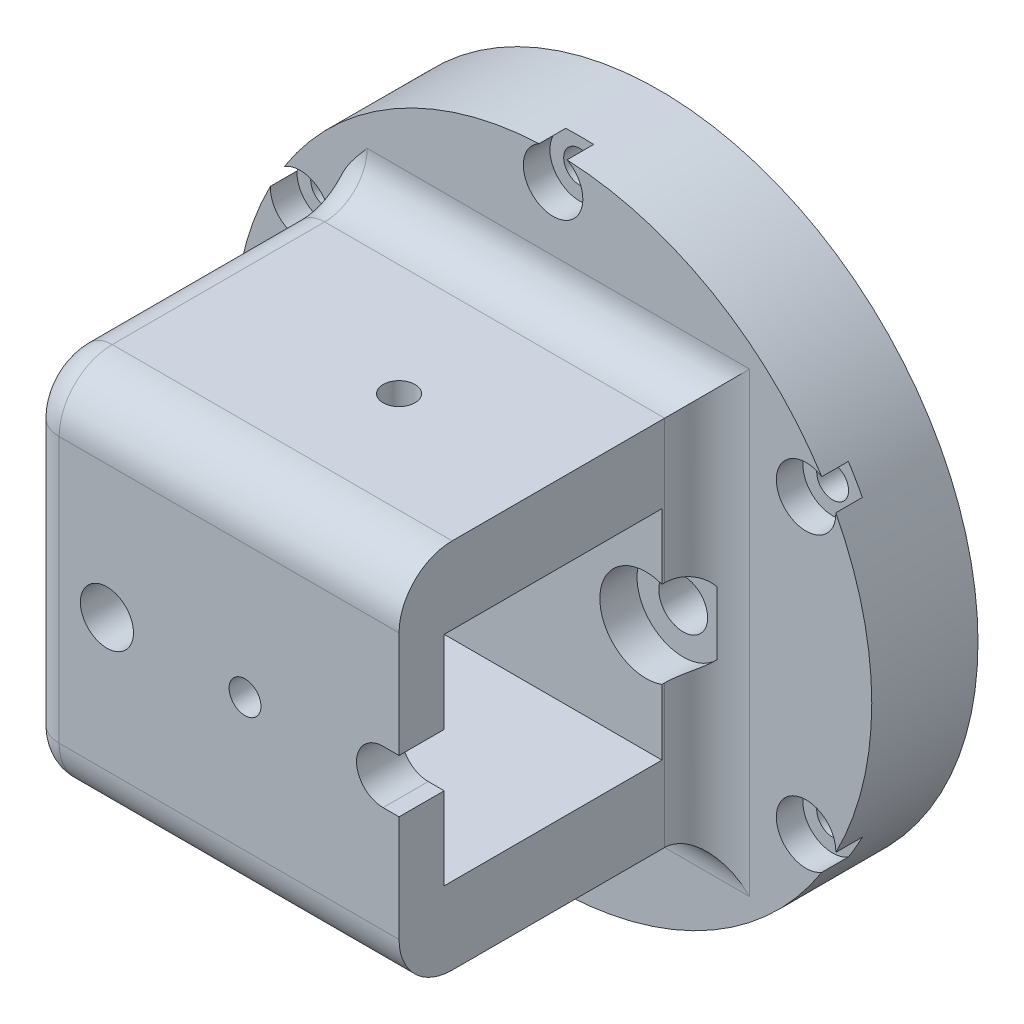
SolidWorks part; units mm, degrees
ref_plane "Piano frontale" through (0, 0, 0) normal (0, 0, 1) x (1, 0, 0)
ref_plane "Piano superiore" through (0, 0, 0) normal (0, 1, 0) x (1, 0, 0)
ref_plane "Piano destro" through (0, 0, 0) normal (1, 0, 0) x (0, 0, -1)
sketch "Schizzo1" plane through (0, 0, 0) normal (0, 0, 1) x (1, 0, 0)
  circle A0 centre (0, 0) radius 30
  circle A1 centre (0, 0) radius 27.5 construction
  circle A2 centre (0, 0) radius 21
  dimension "D1" = 55
  dimension "D2" = 60
  dimension "D3" = 42
extrude "Estrusione-Estrusione1" add sketch "Schizzo1" along normal blind 5
sketch "Schizzo7" plane through (0, 0, 5) normal (0, 0, 1) x (1, 0, 0)
  circle A0 centre (0, 0) radius 30
  circle A1 centre (0, 0) radius 30 construction
extrude "Estrusione-Estrusione2" add sketch "Schizzo7" along normal blind 5
sketch "Schizzo3" plane through (0, 0, 0) normal (0, 0, 1) x (1, 0, 0)
  circle A0 centre (0, 27.5) radius 1.5
  circle A1 centre (0, 0) radius 27.5 construction
  dimension "D1" = 55
  dimension "D2" = 3
extrude "Taglio-Estrusione3" cut sketch "Schizzo3" along normal blind 8
sketch "Schizzo10" plane through (0, 0, 10) normal (0, 0, 1) x (1, 0, 0)
  circle A0 centre (0, 27.5) radius 1.5
  circle A1 centre (0, 27.5) radius 1.5 construction
  circle A2 centre (0, 27.5) radius 2.8
  dimension "D1" = 5.6
extrude "Taglio-Estrusione4" cut sketch "Schizzo10" against normal blind 2.5 contours A2
pattern_circular "RipetizioneCircolare1" count 6 over 360 about axis through (0, 0, 0) along (0, 0, 1) of "Taglio-Estrusione3", "Taglio-Estrusione4"
sketch "Schizzo11" plane through (0, 0, 10) normal (0, 0, 1) x (1, 0, 0)
  line L0 (-14.5, 17.5) -> (14.5, -17.5) construction
  line L1 (-14.5, 17.5) -> (14.5, 17.5)
  line L3 (-14.5, -17.5) -> (14.5, -17.5)
  line L4 (14.5, 17.5) -> (14.5, -17.5)
  line L5 (-14.5, -17.5) -> (-20.5, -17.5)
  line L6 (-20.5, -17.5) -> (-20.5, 17.5)
  line L7 (-20.5, 17.5) -> (-14.5, 17.5)
  line L8 (0, 17.5) -> (0, 0)
  line L9 (0, 0) -> (14.5, 0)
  point P5 (0, -17.5)
  dimension "D1" = 35
  dimension "D2" = 29
  dimension "D3" = 35
extrude "Estrusione-Estrusione4" add sketch "Schizzo11" along normal blind 29 contours L0 L7 L6 L5 L3 | L1 L0 L8 | L8 L9 L4 L1 | L9 L0 L4
sketch "Schizzo12" plane through (14.5, 0, 0) normal (1, 0, 0) x (0, 0, -1)
  line L1 (-14.25, -10.25) -> (-34.75, -10.25)
  line L2 (-14.25, -10.25) -> (-14.25, 10.25)
  line L3 (-14.25, 10.25) -> (-34.75, 10.25)
  line L4 (-34.75, -10.25) -> (-34.75, 10.25)
  line L5 (-14.25, -10.25) -> (-34.75, 10.25) construction
  line L6 (-14.25, 10.25) -> (-34.75, -10.25) construction
  line L8 (-39, 17.5) -> (-10, -17.5) construction
  point P0 (-24.5, 0)
  point P8 (-24.5, 0)
  dimension "D2" = 20.5
  dimension "D3" = 20.5
extrude "Taglio-Estrusione5" cut sketch "Schizzo12" against normal blind 31
fillet "Raccordo3" radius 5 2 edges at (-3, -17.5, 39) (-3, 17.5, 39)
sketch "Schizzo13" plane through (0, -17.5, 0) normal (0, -1, 0) x (1, 0, 0)
  line L0 (-20.5, 10) -> (14.5, 10) construction
  circle A0 centre (0, 24.5) radius 1.5
  dimension "D2" = 3
  dimension "D1" = 14.5
extrude "Taglio-Estrusione6" cut sketch "Schizzo13" against normal through all
sketch "Schizzo14" plane through (0, 0, 39) normal (0, 0, 1) x (1, 0, 0)
  circle A0 centre (0, 0) radius 1.5
  dimension "D1" = 3
extrude "Taglio-Estrusione7" cut sketch "Schizzo14" against normal blind 20
fillet "Raccordo4" radius 4 3 edges at (-3, -17.5, 10) (-3, 17.5, 10) (14.5, 0, 10)
fillet "Raccordo5" radius 3 7 edges at (-20.5, -17.5, 24) (-20.5, -16.0355, 37.5355) (-20.5, 17.5, 24) (-20.5, 16.0355, 37.5355) (-20.5, 0, 39) (-20.5, -18.6716, 11.1716) (-20.5, 18.6716, 11.1716)
ref_plane "Piano1" through (0, 0, 24.5) normal (0, 0, 1) x (1, 0, 0)
sketch "Schizzo15" plane through (0, 0, 5) normal (0, 0, -1) x (-1, 0, 0)
  circle A0 centre (0, 0) radius 13 construction
  circle A2 centre (13, 0) radius 2.3
  circle A4 centre (-13, 0) radius 2.3
  dimension "D1" = 26
  dimension "D2" = 4.6
extrude "Taglio-Estrusione10" cut sketch "Schizzo15" against normal up to surface (9.25 mm away) up to face at (-1, 0, 14.25)
sketch "Schizzo16" plane through (0, 0, 5) normal (0, 0, -1) x (-1, 0, 0)
  circle A0 centre (0, 0) radius 16.25
  circle A1 centre (-13, 0) radius 2.3
  circle A3 centre (13, 0) radius 2.3
  circle A6 centre (-13, 0) radius 2.3 construction
  dimension "D1" = 32.5
extrude "Taglio-Estrusione11" cut sketch "Schizzo16" against normal blind 2
sketch "Schizzo17" plane through (0, 0, 14.25) normal (0, 0, 1) x (1, 0, 0)
  circle A0 centre (-13, 0) radius 4.35
  circle A1 centre (13, 0) radius 4.35
  dimension "D1" = 8.7
  dimension "D2" = 8.7
extrude "Taglio-Estrusione12" cut sketch "Schizzo17" against normal blind 3.5
sketch "Schizzo18" plane through (0, 0, 14.25) normal (0, 0, 1) x (1, 0, 0)
  circle A0 centre (-13, 0) radius 4.35
  arc A1 (-16.5, -2.5831) -> (-16.5, 2.5831) centre (-13, 0) ccw construction
  circle A2 centre (13, 0) radius 4.35
  arc A3 (14.5, 4.0832) -> (14.5, -4.0832) centre (13, 0) ccw construction
extrude "Taglio-Estrusione13" cut sketch "Schizzo18" along normal up to surface (20.5 mm away) up to face at (1.5, 0, 34.75)
sketch "Schizzo20" plane through (0, 0, 14.25) normal (0, 0, 1) x (1, 0, 0)
  line L0 (13, 2.5) -> (15.5, 2.5)
  line L1 (15.5, 2.5) -> (15.5, -2.5)
  line L2 (15.5, -2.5) -> (13, -2.5)
  arc A0 (13, 2.5) -> (13, -2.5) centre (13, 0) ccw
  circle A1 centre (-13, 0) radius 2.5
  dimension "D1" = 5
  dimension "D2" = 5
extrude "Taglio-Estrusione14" cut sketch "Schizzo20" along normal through all
